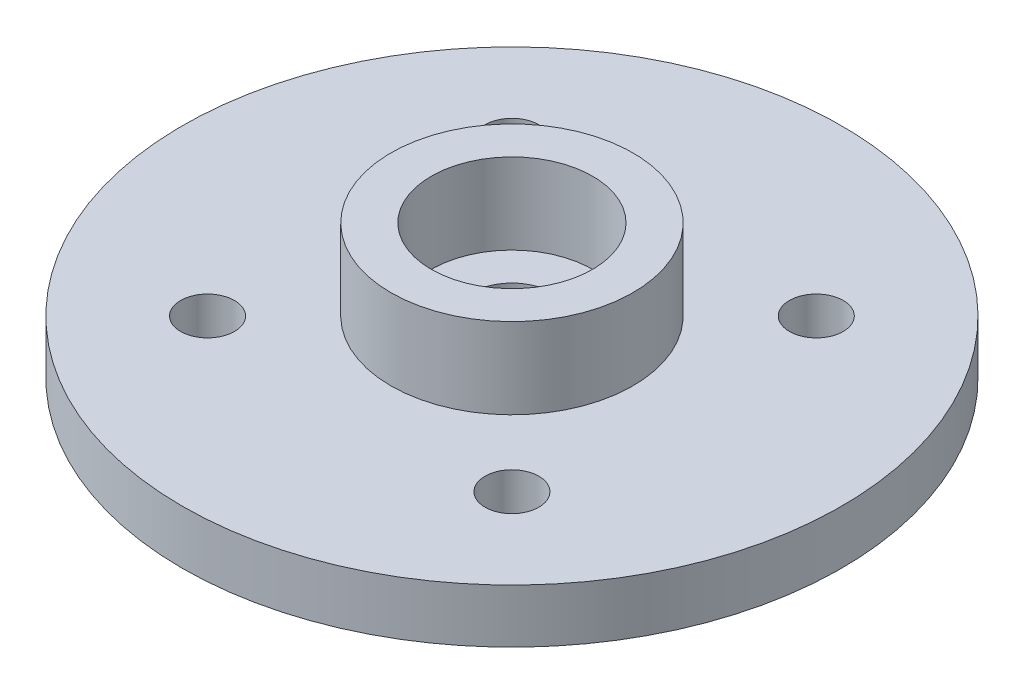
SolidWorks part; units mm, degrees
ref_plane "前视基准面" through (0, 0, 0) normal (0, 0, 1) x (1, 0, 0)
ref_plane "上视基准面" through (0, 0, 0) normal (0, 1, 0) x (1, 0, 0)
ref_plane "右视基准面" through (0, 0, 0) normal (1, 0, 0) x (0, 0, -1)
sketch "Sketch1" plane through (0, 0, 0) normal (0, 1, 0) x (1, 0, 0)
  line L1 (-5.6569, -5.6569) -> (5.6569, -5.6569) construction
  line L2 (-5.6569, -5.6569) -> (-5.6569, 5.6569) construction
  line L3 (-5.6569, 5.6569) -> (5.6569, 5.6569) construction
  line L4 (5.6569, -5.6569) -> (5.6569, 5.6569) construction
  line L5 (-5.6569, -5.6569) -> (5.6569, 5.6569) construction
  line L6 (-5.6569, 5.6569) -> (5.6569, -5.6569) construction
  circle A0 centre (0, 0) radius 12.25
  circle A1 centre (-5.6569, 5.6569) radius 1
  circle A2 centre (5.6569, 5.6569) radius 1
  circle A3 centre (-5.6569, -5.6569) radius 1
  circle A4 centre (5.6569, -5.6569) radius 1
  circle A5 centre (0, 0) radius 1.5
  dimension "D1" = 24.5
  dimension "D3" = 2
  dimension "D4" = 3
  dimension "D2" = 16
extrude "Boss-Extrude1" add sketch "Sketch1" along normal blind 2
sketch "Sketch2" plane through (0, 2, 0) normal (0, 1, 0) x (1, 0, 0)
  circle A0 centre (0, 0) radius 4.5
  circle A1 centre (0, 0) radius 3
  dimension "D1" = 6
  dimension "D2" = 9
extrude "Boss-Extrude2" add sketch "Sketch2" along normal blind 3
